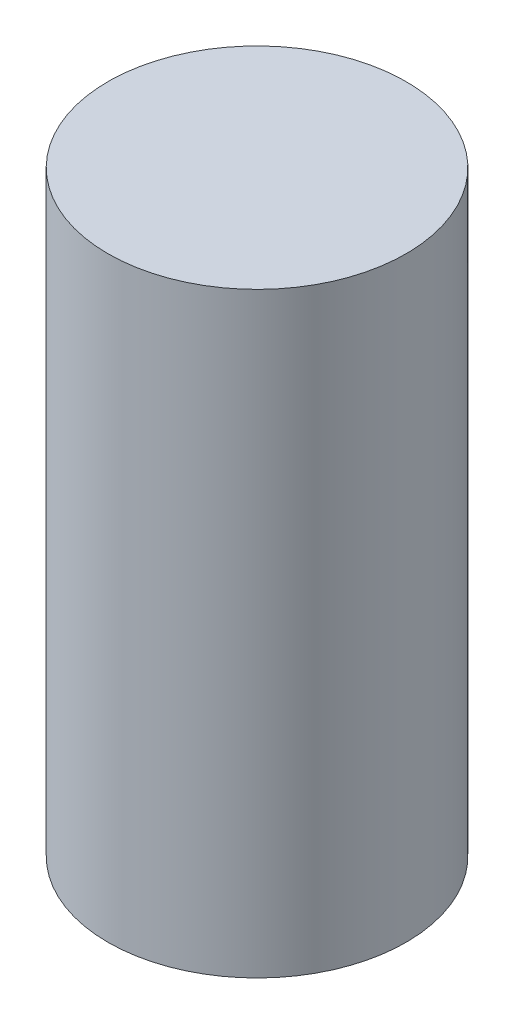
SolidWorks part; units mm, degrees
ref_plane "前视基准面" through (0, 0, 0) normal (0, 0, 1) x (1, 0, 0)
ref_plane "上视基准面" through (0, 0, 0) normal (0, 1, 0) x (1, 0, 0)
ref_plane "右视基准面" through (0, 0, 0) normal (1, 0, 0) x (0, 0, -1)
sketch "草图1" plane through (0, 0, 0) normal (0, 1, 0) x (1, 0, 0)
  circle A0 centre (0, 0) radius 100
  dimension "D1" = 200
extrude "凸台-拉伸1" add sketch "草图1" along normal blind 400
